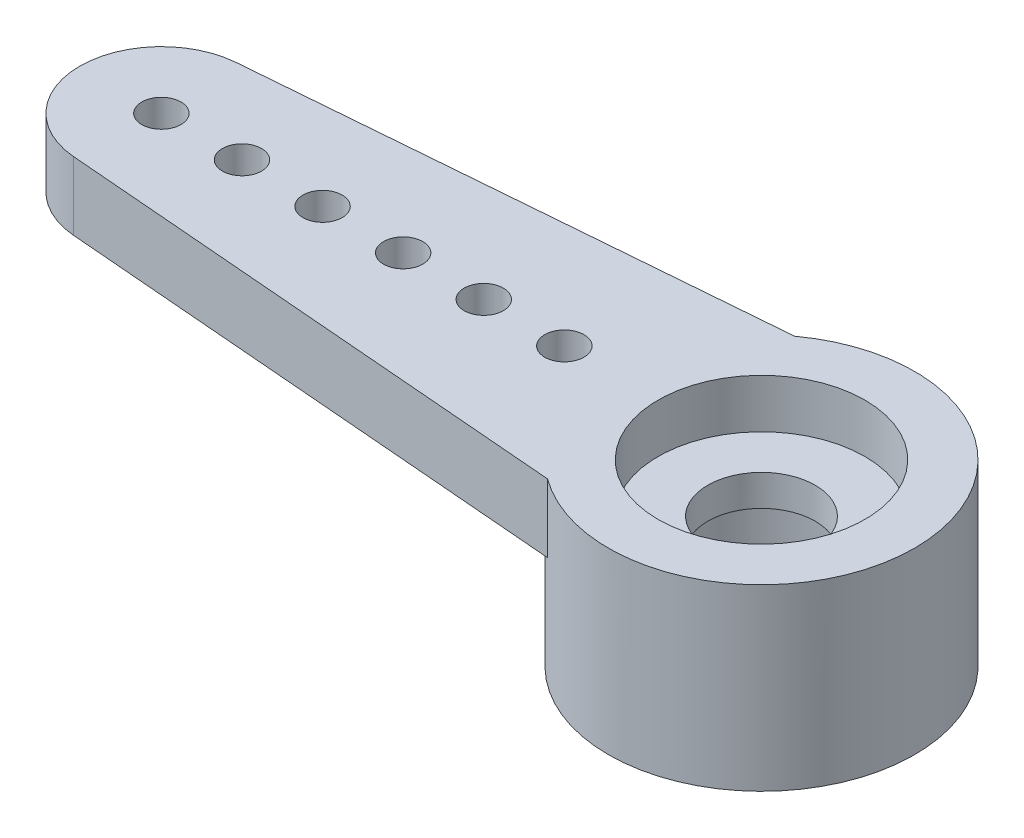
SolidWorks part; units mm, degrees
material "Nylon 101"
ref_plane "Front Plane" through (0, 0, 0) normal (0, 0, 1) x (1, 0, 0)
ref_plane "Top Plane" through (0, 0, 0) normal (0, 1, 0) x (1, 0, 0)
ref_plane "Right Plane" through (0, 0, 0) normal (1, 0, 0) x (0, 0, -1)
sketch "Sketch18" plane through (0, 0, 0) normal (0, 1, 0) x (1, 0, 0)
  line L0 (-16.1163, 0) -> (3.6195, 0) construction
  line L1 (-14.3431, 1.924) -> (-2.1374, 2.921)
  line L2 (-14.3431, -1.924) -> (-2.1374, -2.921)
  arc A0 (-2.1374, -2.921) -> (-2.1374, 2.921) centre (0, 0) ccw
  arc A1 (-14.3431, 1.924) -> (-14.3431, -1.924) centre (-14.1859, 0) ccw
  dimension "D1" = 1.9304
  dimension "D2" = 3.6195
  dimension "D3" = 19.7358
  dimension "D4" = 5.842
extrude "Extrude17" add sketch "Sketch18" along normal blind 1.6129
sketch "Sketch19" plane through (0, 1.6129, 0) normal (0, 1, 0) x (1, 0, 0)
  circle A0 centre (0, 0) radius 3.6195
  arc A1 (-2.1374, -2.921) -> (-2.1374, 2.921) centre (0, 0) ccw construction
extrude "Extrude19" add sketch "Sketch19" against normal blind 4.2291
sketch "Sketch20" plane through (0, 1.6129, 0) normal (0, 1, 0) x (1, 0, 0)
  line L0 (-14.1859, 0) -> (-12.2809, 0) construction
  line L1 (-12.2809, 0) -> (-10.3759, 0) construction
  line L2 (-10.3759, 0) -> (-8.4709, 0) construction
  line L3 (-8.4709, 0) -> (-6.5659, 0) construction
  line L4 (-6.5659, 0) -> (-4.6609, 0) construction
  line L5 (-4.6609, 0) -> (-2.7559, 0) construction
  line L6 (-2.7559, 0) -> (0, 0) construction
  circle A0 centre (-14.1859, 0) radius 0.4636
  circle A1 centre (0, 0) radius 1.27
  circle A3 centre (-4.6609, 0) radius 0.4636
  circle A4 centre (-6.5659, 0) radius 0.4636
  circle A5 centre (-8.4709, 0) radius 0.4636
  circle A6 centre (-10.3759, 0) radius 0.4636
  circle A7 centre (-12.2809, 0) radius 0.4636
  dimension "D1" = 0.9271
  dimension "D3" = 2.54
  dimension "D2" = 1.905
extrude "Extrude20" cut sketch "Sketch20" against normal through all
sketch "Sketch21" plane through (0, 1.6129, 0) normal (0, 1, 0) x (1, 0, 0)
  circle A0 centre (0, 0) radius 2.4447
  dimension "D1" = 4.8895
extrude "Extrude21" cut sketch "Sketch21" against normal blind 1.1557
sketch "Sketch22" plane through (0, -2.6162, 0) normal (0, -1, 0) x (1, 0, 0)
  circle A0 centre (0, 0) radius 2.286
  dimension "D1" = 4.572
extrude "Extrude22" cut sketch "Sketch22" against normal blind 2.3368
